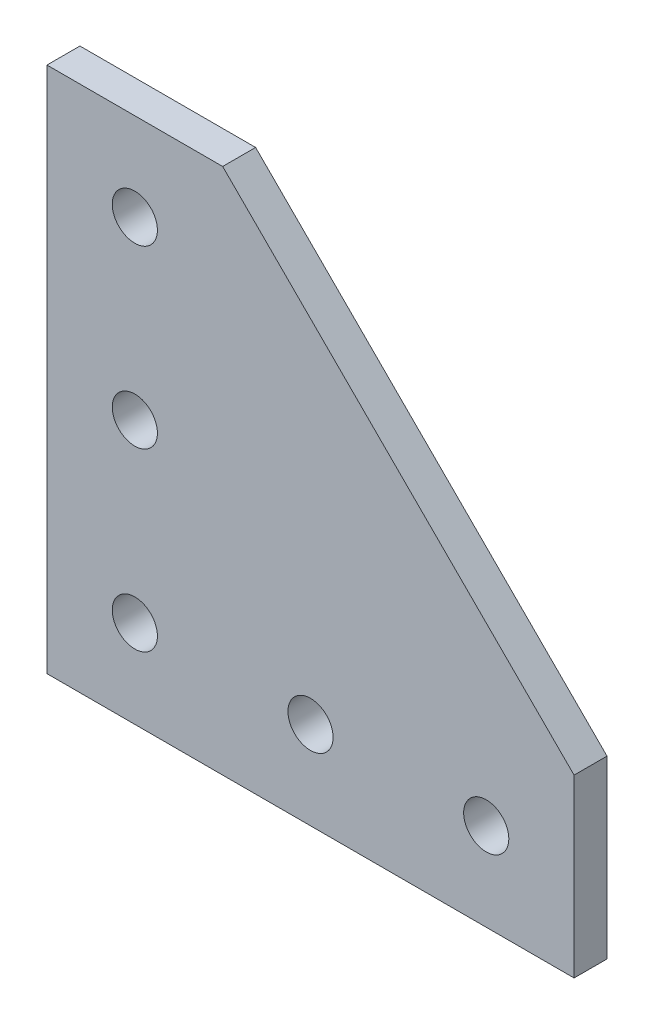
SolidWorks part; units mm, degrees
material "6061-T6 (SS)"
ref_plane "Front Plane" through (0, 0, 0) normal (0, 0, 1) x (1, 0, 0)
ref_plane "Top Plane" through (0, 0, 0) normal (0, 1, 0) x (1, 0, 0)
ref_plane "Right Plane" through (0, 0, 0) normal (1, 0, 0) x (0, 0, -1)
sketch "Sketch1" plane through (0, 0, 0) normal (0, 0, 1) x (1, 0, 0)
  line L0 (0, 0) -> (0, 76.2)
  line L1 (12.7, 12.7) -> (38.1, 12.7) construction
  line L2 (38.1, 12.7) -> (63.5, 12.7) construction
  line L3 (12.7, 12.7) -> (12.7, 38.1) construction
  line L4 (76.2, 25.4) -> (25.4, 76.2)
  line L5 (76.2, 0) -> (0, 0)
  line L6 (12.7, 38.1) -> (12.7, 63.5) construction
  line L7 (76.2, 25.4) -> (76.2, 0)
  line L8 (0, 76.2) -> (25.4, 76.2)
  circle A0 centre (12.7, 12.7) radius 3.2639
  circle A1 centre (38.1, 12.7) radius 3.2639
  circle A2 centre (63.5, 12.7) radius 3.2639
  circle A3 centre (12.7, 38.1) radius 3.2639
  circle A4 centre (12.7, 63.5) radius 3.2639
  dimension "D1" = 25.4
  dimension "E" = 6.5278
  dimension "D2" = 12.7
  dimension "C" = 25.4
  dimension "D3" = 12.7
  dimension "B" = 76.2
extrude "Boss-Extrude1" add sketch "Sketch1" along normal mid plane 4.7625
sketch "Sketch2" plane through (0, 0, 2.3813) normal (0, 0, 1) x (1, 0, 0)
  line L0 (0, 50.8) -> (50.8, 50.8)
  line L1 (0, 76.2) -> (0, 0) construction
  line L2 (76.2, 25.4) -> (25.4, 76.2) construction
  line L3 (50.8, 50.8) -> (25.4, 76.2)
  line L4 (25.4, 76.2) -> (0, 76.2)
  line L5 (0, 76.2) -> (0, 50.8)
  line L6 (12.7, 63.5) -> (12.7, 38.1) construction
  point P14 (12.7, 50.8)
extrude "Cut-Extrude1" [suppressed] cut sketch "Sketch2" against normal through all both and the other way through all
